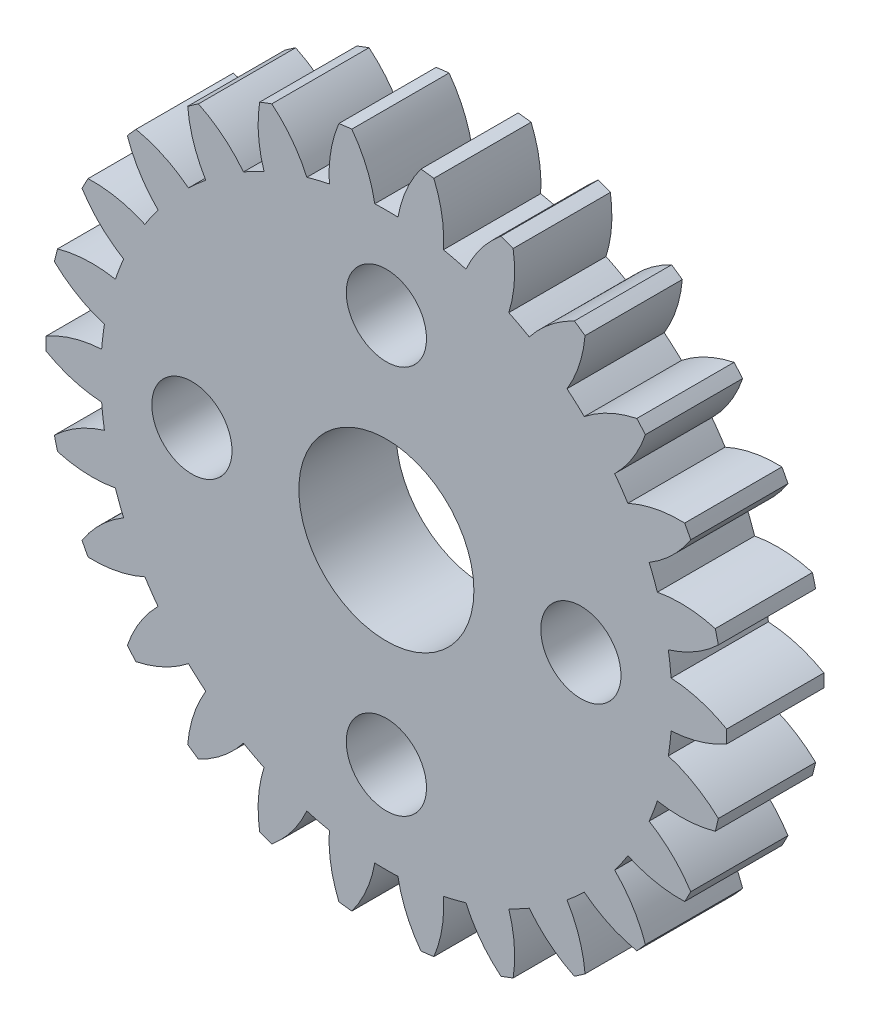
SolidWorks part; units mm, degrees
material "鑄碳鋼"
ref_plane "前基準面" through (0, 0, 0) normal (0, 0, 1) x (1, 0, 0)
ref_plane "上基準面" through (0, 0, 0) normal (0, 1, 0) x (1, 0, 0)
ref_plane "右基準面" through (0, 0, 0) normal (1, 0, 0) x (0, 0, -1)
sketch "草圖1" plane through (0, 0, 0) normal (0, 0, 1) x (1, 0, 0)
  circle A0 centre (0, 0) radius 14
  dimension "D1" = 28
extrude "填料-伸長1" add sketch "草圖1" along normal blind 4
sketch "草圖4" plane through (0, 0, 4) normal (0, 0, 1) x (1, 0, 0)
  line L0 (-1.4216, 13.9276) -> (0, 0) construction
  line L1 (0, 0) -> (1.4216, 13.9276) construction
  line L2 (-0.477, 11.7403) -> (0, 0) construction
  line L3 (0, 0) -> (0.477, 11.7403) construction
  arc A0 (-1.4216, 13.9276) -> (1.4216, 13.9276) centre (0, 0) cw
  circle A1 centre (0, 0) radius 14 construction
  arc A2 (-0.477, 11.7403) -> (0.477, 11.7403) centre (0, 0) cw
  arc A3 (-1.4216, 13.9276) -> (-0.477, 11.7403) centre (-5.5962, 10.8272) cw
  arc A4 (1.4216, 13.9276) -> (0.477, 11.7403) centre (5.5962, 10.8272) ccw
  circle A5 centre (0, 0) radius 13 construction
  point P8 (0, 14)
  point P9 (0, 11.75)
  dimension "D1" = 5.2
  dimension "D2" = 5.2
  dimension "D3" = 11.75
  dimension "D6" = 26
  dimension "D4" = 4.653
  dimension "D5" = 11.656
extrude "除料-伸長1" cut sketch "草圖4" against normal up to next (4 mm away)
pattern_circular "環狀複製排列1" count 26 over 360 about axis through (0, 0, 0) along (0, 0, 1) of "除料-伸長1"
sketch "草圖5" plane through (0, 0, 4) normal (0, 0, 1) x (1, 0, 0)
  circle A0 centre (0, 0) radius 3.6
  circle A1 centre (0, 0) radius 8 construction
  circle A2 centre (0, 8) radius 1.65
  circle A3 centre (8, 0) radius 1.65
  circle A4 centre (0, -8) radius 1.65
  circle A5 centre (-8, 0) radius 1.65
  dimension "D1" = 7.2
  dimension "D2" = 16
  dimension "D3" = 3.3
  dimension "D6" = 90
  dimension "D5" = 8
  dimension "D4" = 4
extrude "除料-伸長2" cut sketch "草圖5" against normal up to next
